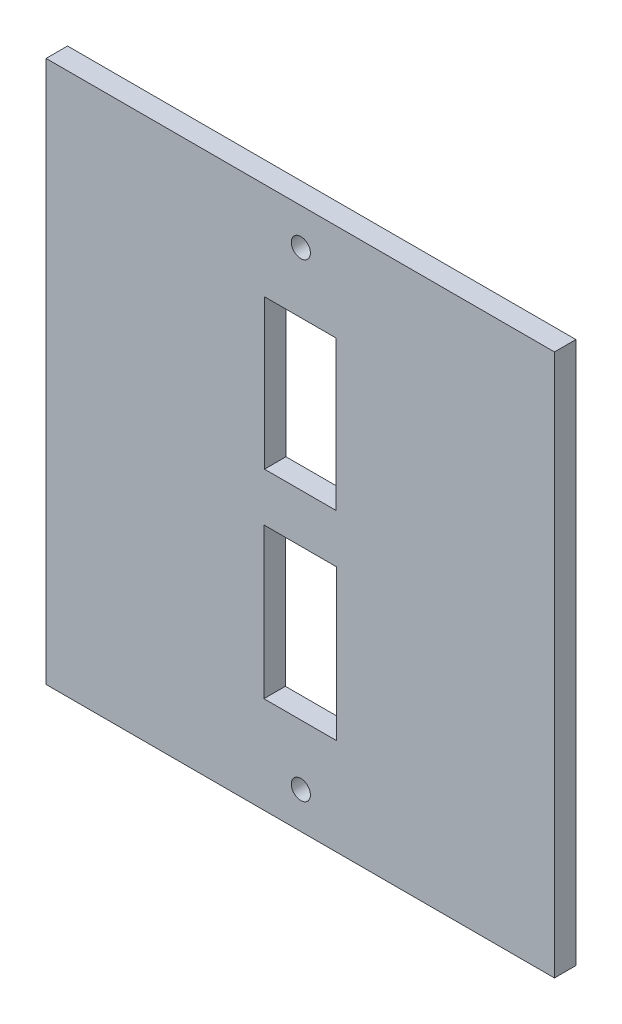
SolidWorks part; units mm, degrees
material "Maple"
ref_plane "Front Plane" through (0, 0, 0) normal (0, 0, 1) x (1, 0, 0)
ref_plane "Top Plane" through (0, 0, 0) normal (0, 1, 0) x (1, 0, 0)
ref_plane "Right Plane" through (0, 0, 0) normal (1, 0, 0) x (0, 0, -1)
sketch "Sketch1" plane through (0, 0, 0) normal (0, 0, 1) x (1, 0, 0)
  line L0 (0, 0) -> (0, 40.085) construction
  line L1 (-37.585, 40.085) -> (37.585, 40.085)
  line L2 (-37.585, 40.085) -> (-37.585, -40.085)
  line L3 (-37.585, -40.085) -> (37.585, -40.085)
  line L4 (37.585, 40.085) -> (37.585, -40.085)
  line L5 (-37.585, 40.085) -> (37.585, -40.085) construction
  line L6 (-37.585, -40.085) -> (37.585, 40.085) construction
  line L7 (0, 0) -> (12.3244, 0) construction
  line L8 (-5.375, 3.55) -> (5.375, 3.55) construction
  line L9 (-5.375, 3.55) -> (-5.375, 25.8) construction
  line L10 (-5.375, 25.8) -> (5.375, 25.8) construction
  line L11 (5.375, 3.55) -> (5.375, 25.8) construction
  line L12 (-5.375, 3.55) -> (5.375, 25.8) construction
  line L13 (-5.375, 25.8) -> (5.375, 3.55) construction
  line L14 (-5.375, -25.8) -> (5.375, -25.8)
  line L15 (5.375, -3.55) -> (5.375, -25.8)
  line L16 (-5.375, -3.55) -> (5.375, -3.55)
  line L17 (-5.375, -3.55) -> (-5.375, -25.8)
  line L18 (-5.29, 25.715) -> (5.29, 25.715)
  line L19 (5.29, 3.635) -> (5.29, 25.715)
  line L20 (-5.29, 3.635) -> (5.29, 3.635)
  line L21 (-5.29, 3.635) -> (-5.29, 25.715)
  line L22 (-5.46, -3.465) -> (5.46, -3.465) construction
  line L23 (5.46, -3.465) -> (5.46, -25.885) construction
  line L24 (-5.46, -25.885) -> (5.46, -25.885) construction
  line L25 (-5.46, -3.465) -> (-5.46, -25.885) construction
  point P0 (0, 0)
  point P8 (0, 3.55)
  point P9 (0, 25.8)
  point P10 (0, 14.675)
  point P11 (0, 14.675)
  dimension "D1" = 75.17
  dimension "D2" = 80.17
  dimension "D3" = 3.55
  dimension "D4" = 22.25
  dimension "D5" = 11.125
  dimension "D6" = 10.75
  dimension "D7" = 0.085
  dimension "D8" = 0.085
extrude "Boss-Extrude1" add sketch "Sketch1" along normal blind 3.175
sketch "Sketch2" plane through (0, 0, 3.175) normal (0, 0, 1) x (1, 0, 0)
  line L4 (-32.1967, 34.6967) -> (0.085, 34.6967) construction
  line L8 (-32.1967, 34.6967) -> (-37.5, 40) construction
  line L10 (-37.5, 40) -> (-37.5, -40.085)
  line L11 (37.585, 40) -> (-37.5, 40)
  line L12 (-37.5, 40) -> (-37.5, -40.085) construction
  line L13 (37.585, 40) -> (-37.5, 40) construction
  circle A0 centre (-32.1967, 34.6967) radius 1.415 construction
  circle A1 centre (0.085, 34.6967) radius 1.415
  circle A2 centre (0.085, -34.6967) radius 1.415
  dimension "D3" = 2.83
  dimension "D4" = 2.83
  dimension "D1" = 0.085
  dimension "D2" = 7.5
  dimension "D5" = 45
extrude "Cut-Extrude1" cut sketch "Sketch2" against normal through all
equation "\"length\"= 75"
equation "\"width\"= 80mm"
equation "\"depth\"= 6.35"
equation "\"kerf\"= 0.17 / 2"
